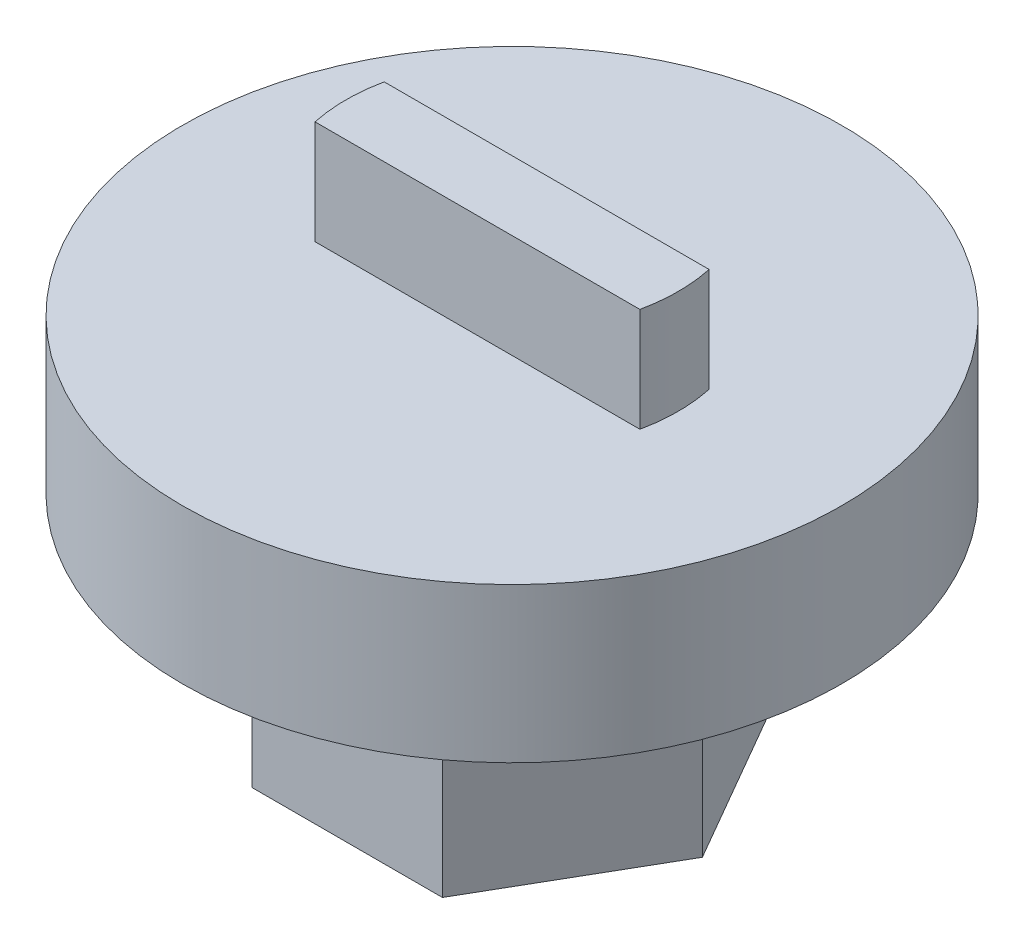
SolidWorks part; units mm, degrees
ref_plane "Front" through (0, 0, 0) normal (0, 0, 1) x (1, 0, 0)
ref_plane "Top" through (0, 0, 0) normal (0, 1, 0) x (1, 0, 0)
ref_plane "Right" through (0, 0, 0) normal (1, 0, 0) x (0, 0, -1)
sketch "Sketch1" plane through (0, 0, 0) normal (0, 1, 0) x (1, 0, 0)
  line L1 (1.3748, 2.3813) -> (-1.3748, 2.3812)
  line L2 (-1.3748, 2.3812) -> (-2.7496, 0)
  line L3 (-2.7496, 0) -> (-1.3748, -2.3813)
  line L4 (-1.3748, -2.3813) -> (1.3748, -2.3813)
  line L5 (1.3748, -2.3813) -> (2.7496, 0)
  line L6 (2.7496, 0) -> (1.3748, 2.3813)
  circle A0 centre (0, 0) radius 2.3813 construction
  dimension "D1" = 4.7625
extrude "Boss-Extrude1" add sketch "Sketch1" along normal blind 3.175
sketch "Sketch2" plane through (0, 3.175, 0) normal (0, 1, 0) x (1, 0, 0)
  circle A0 centre (0, 0) radius 4.7625
  dimension "D1" = 9.525
extrude "Boss-Extrude2" add sketch "Sketch2" along normal blind 2.2301
sketch "Sketch3" plane through (0, 5.4051, 0) normal (0, 1, 0) x (1, 0, 0)
  line L0 (-2.3473, 0.5) -> (2.3473, 0.5)
  line L1 (2.3473, -0.5) -> (-2.3473, -0.5)
  line L2 (0, 0.5) -> (0, -0.5) construction
  arc A0 (-2.3473, 0.5) -> (-2.3473, -0.5) centre (0, 0) ccw
  arc A1 (2.3473, -0.5) -> (2.3473, 0.5) centre (0, 0) ccw
  dimension "D1" = 4.8
  dimension "D2" = 1
extrude "Boss-Extrude3" add sketch "Sketch3" along normal blind 1.5
